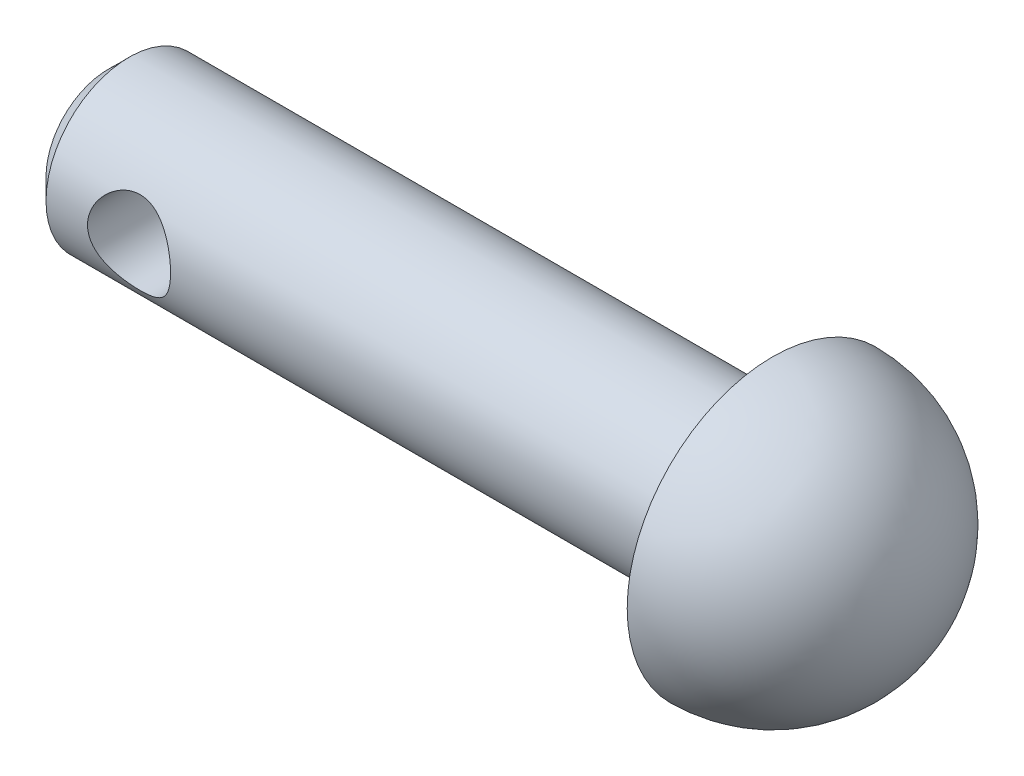
SolidWorks part; units mm, degrees
ref_plane "Front Plane" through (0, 0, 0) normal (0, 0, 1) x (1, 0, 0)
ref_plane "Top Plane" through (0, 0, 0) normal (0, 1, 0) x (1, 0, 0)
ref_plane "Right Plane" through (0, 0, 0) normal (1, 0, 0) x (0, 0, -1)
sketch "Sketch1" plane through (0, 0, 0) normal (0, 0, 1) x (1, 0, 0)
  line L0 (-10.0707, 0) -> (25.7672, 0) construction
  line L1 (-6.9896, 0) -> (-6.9896, 2)
  line L2 (-6.9896, 2) -> (9.0104, 2)
  line L3 (9.0104, 2) -> (9.0104, 3.5)
  line L4 (12.5104, 0) -> (-6.9896, 0)
  arc A0 (12.5104, 0) -> (9.0104, 3.5) centre (9.0104, 0) ccw
  dimension "D3" = 3.5
  dimension "D1" = 16
  dimension "D2" = 2
revolve "Revolve1" add sketch "Sketch1" angle 360 about L0
chamfer "Chamfer1" distance 0.5 angle 45 1 edges at (-6.9896, 0, 2)
sketch "Sketch2" plane through (0, 0, 0) normal (0, 0, 1) x (1, 0, 0)
  line L0 (9.0104, 3.5) -> (9.0104, -3.5) construction
  circle A0 centre (-4.4896, 0) radius 1
  dimension "D1" = 2
  dimension "D2" = 13.5
extrude "Cut-Extrude1" cut sketch "Sketch2" against normal through all both and the other way through all
